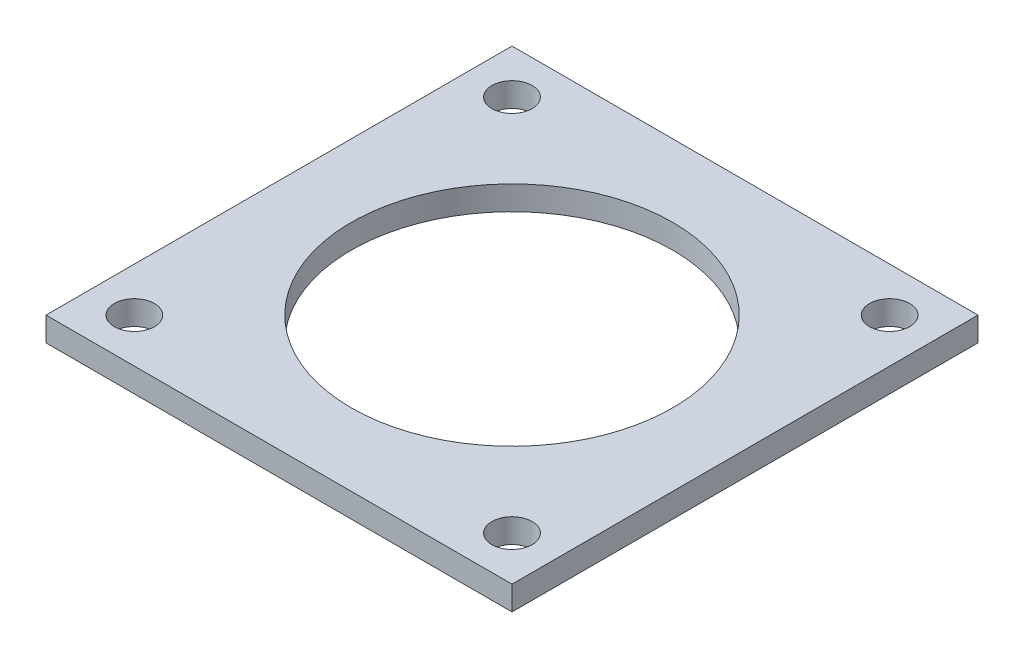
SolidWorks part; units mm, degrees
ref_plane "Front Plane" through (0, 0, 0) normal (0, 0, 1) x (1, 0, 0)
ref_plane "Top Plane" through (0, 0, 0) normal (0, 1, 0) x (1, 0, 0)
ref_plane "Right Plane" through (0, 0, 0) normal (1, 0, 0) x (0, 0, -1)
sketch "Sketch1" plane through (0, 0, 0) normal (0, 1, 0) x (1, 0, 0)
  line L0 (0, 0) -> (5.5, 0) construction
  line L1 (0, 0) -> (58, 0)
  line L2 (0, 0) -> (0, -58)
  line L3 (0, -58) -> (58, -58)
  line L4 (58, 0) -> (58, -58)
  line L5 (5.5, 0) -> (5.5, -5.5) construction
  line L6 (29, 0) -> (29, -58) construction
  line L7 (0, -29) -> (58, -29) construction
  circle A0 centre (29, -29) radius 20
  circle A1 centre (5.5, -5.5) radius 2.5
  circle A2 centre (52.5, -5.5) radius 2.5
  circle A3 centre (52.5, -52.5) radius 2.5
  circle A4 centre (5.5, -52.5) radius 2.5
  dimension "D2" = 40
  dimension "D5" = 5
  dimension "D1" = 58
  dimension "D3" = 5.5
  dimension "D4" = 5.5
extrude "Boss-Extrude1" add sketch "Sketch1" along normal blind 3
